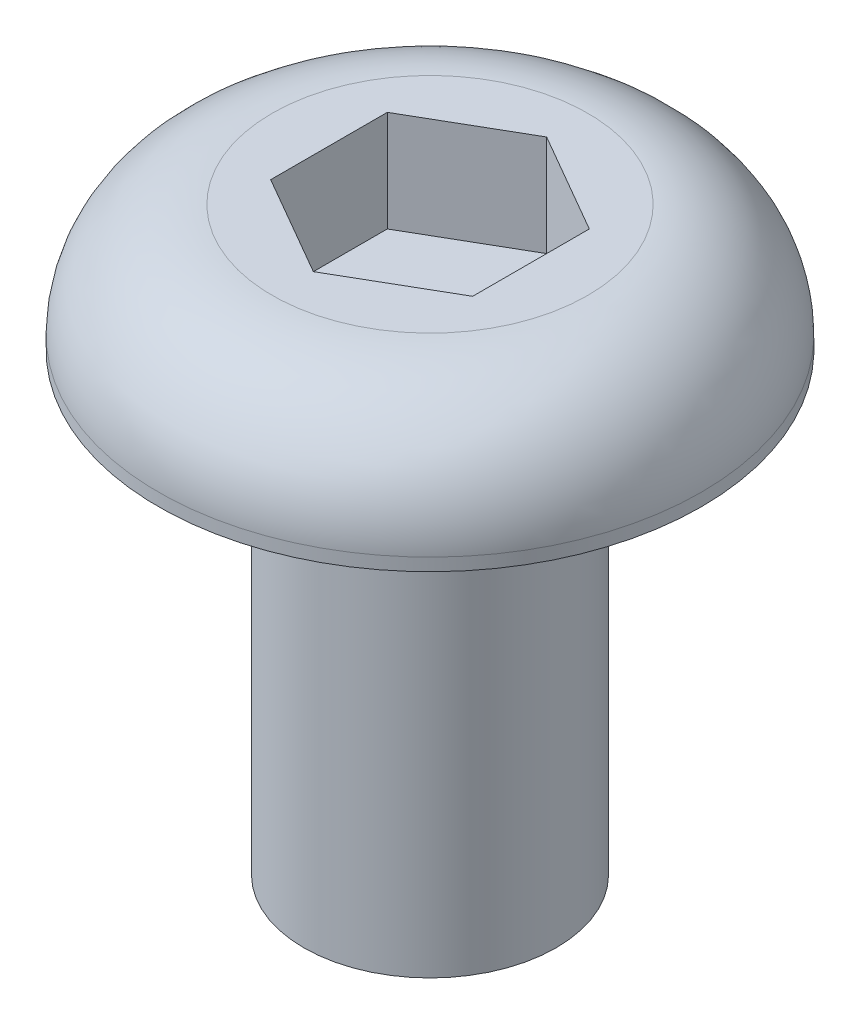
SolidWorks part; units mm, degrees
ref_plane "Plano frontal" through (0, 0, 0) normal (0, 0, 1) x (1, 0, 0)
ref_plane "Plano superior" through (0, 0, 0) normal (0, 1, 0) x (1, 0, 0)
ref_plane "Plano direito" through (0, 0, 0) normal (1, 0, 0) x (0, 0, -1)
sketch "Esboço1" plane through (0, 0, 0) normal (0, 0, 1) x (1, 0, 0)
  line L0 (0, 0) -> (5, 0)
  line L1 (5, 0) -> (5, 18)
  line L2 (5, 18) -> (10.75, 18)
  line L3 (10.75, 18) -> (10.75, 18.5)
  line L4 (6.25, 23) -> (0, 23)
  line L5 (0, 23) -> (0, 0) construction
  line L6 (0, 0) -> (0, 23)
  arc A0 (10.75, 18.5) -> (6.25, 23) centre (6.25, 18.5) ccw
  dimension "D1" = 10
  dimension "D2" = 18
  dimension "D3" = 0.5
  dimension "D4" = 12.5
  dimension "D5" = 23
revolve "Revolução1" add sketch "Esboço1" angle 360 about L5
sketch "Esboço2" plane through (0, 23, 0) normal (0, 1, 0) x (1, 0, 0)
  line L1 (0, 4.6188) -> (-4, 2.3094)
  line L2 (-4, 2.3094) -> (-4, -2.3094)
  line L3 (-4, -2.3094) -> (0, -4.6188)
  line L4 (0, -4.6188) -> (4, -2.3094)
  line L5 (4, -2.3094) -> (4, 2.3094)
  line L6 (4, 2.3094) -> (0, 4.6188)
  circle A0 centre (0, 0) radius 4 construction
  dimension "D1" = 8
extrude "Corte-extrusão1" cut sketch "Esboço2" against normal blind 4
